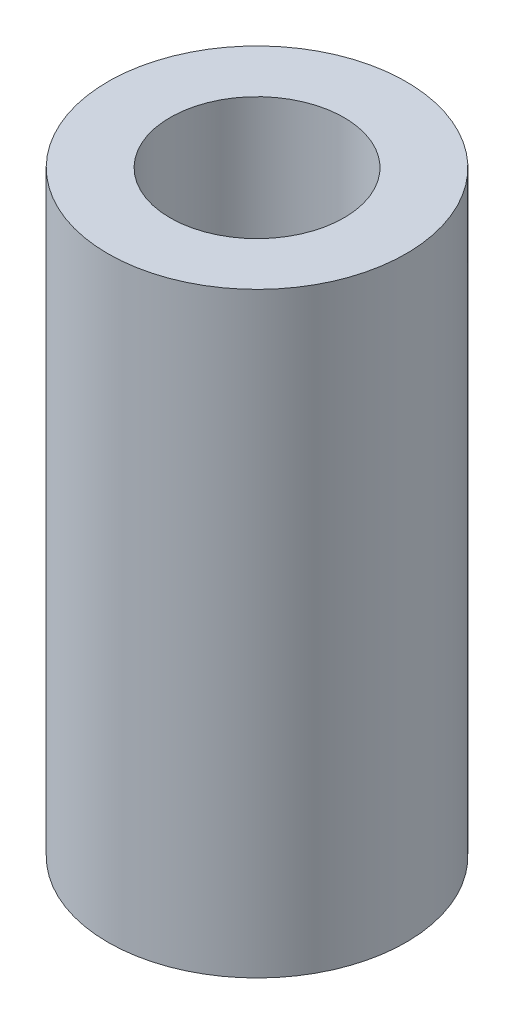
SolidWorks part; units mm, degrees
ref_plane "Front Plane" through (0, 0, 0) normal (0, 0, 1) x (1, 0, 0)
ref_plane "Top Plane" through (0, 0, 0) normal (0, 1, 0) x (1, 0, 0)
ref_plane "Right Plane" through (0, 0, 0) normal (1, 0, 0) x (0, 0, -1)
sketch "Sketch1" plane through (0, 0, 0) normal (0, 1, 0) x (1, 0, 0)
  circle A0 centre (0, 0) radius 3
  circle A1 centre (0, 0) radius 1.75
  dimension "D1" = 6
  dimension "D2" = 3.5
extrude "Boss-Extrude1" add sketch "Sketch1" along normal blind 12
